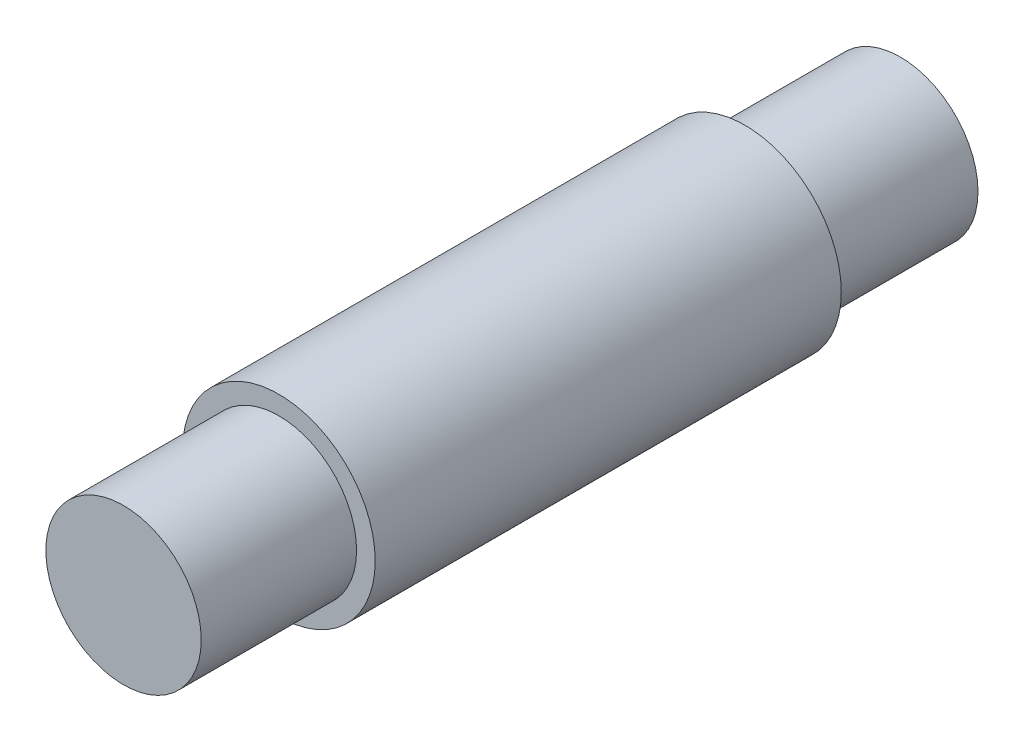
SolidWorks part; units mm, degrees
material "1023 Carbon Steel Sheet (SS)"
ref_plane "Front Plane" through (0, 0, 0) normal (0, 0, 1) x (1, 0, 0)
ref_plane "Top Plane" through (0, 0, 0) normal (0, 1, 0) x (1, 0, 0)
ref_plane "Right Plane" through (0, 0, 0) normal (1, 0, 0) x (0, 0, -1)
sketch "Sketch2" plane through (0, 0, 0) normal (0, 0, 1) x (1, 0, 0)
  circle A0 centre (0, 0) radius 1.55
  dimension "D1" = 3.1
extrude "Boss-Extrude2" add sketch "Sketch2" along normal blind 3.75
sketch "Sketch4" plane through (0, 0, 3.75) normal (0, 0, 1) x (1, 0, 0)
  circle A0 centre (0, 0) radius 1.25
  dimension "D1" = 2.5
extrude "Boss-Extrude3" add sketch "Sketch4" along normal blind 2.5
mirror "Mirror3" about plane through (0, 0, 0) normal (0, 0, 1) of "Boss-Extrude2", "Boss-Extrude3"
